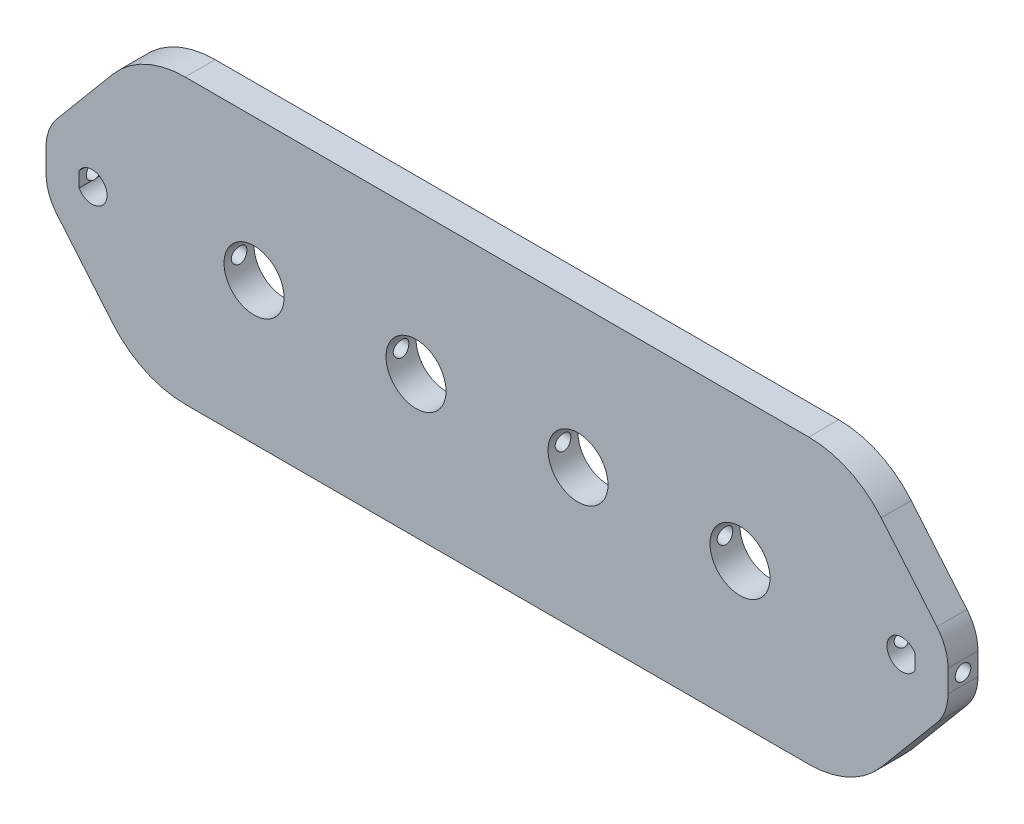
SolidWorks part; units mm, degrees
ref_plane "Front Plane" through (0, 0, 0) normal (0, 0, 1) x (1, 0, 0)
ref_plane "Top Plane" through (0, 0, 0) normal (0, 1, 0) x (1, 0, 0)
ref_plane "Right Plane" through (0, 0, 0) normal (1, 0, 0) x (0, 0, -1)
sketch "Sketch1" plane through (0, 0, 0) normal (0, 0, 1) x (1, 0, 0)
  line L0 (-85.725, 0) -> (85.725, 0) construction
  line L1 (-85.725, 30) -> (85.725, 30)
  line L2 (-85.725, -30) -> (85.725, -30)
  line L3 (0, 30) -> (0, -30) construction
  line L4 (-75.3362, 30) -> (-95.4746, 6)
  line L5 (-95.4746, 6) -> (-95.4746, -6)
  line L6 (-95.4746, -6) -> (-75.3362, -30)
  line L7 (-88.4746, -0.7777) -> (-88.4746, -1.5875) construction
  line L8 (-88.4746, -0.7777) -> (-88.4746, 0.7777) construction
  line L13 (88.4746, 1.5875) -> (88.4746, -1.5875)
  line L14 (-88.4746, 1.5875) -> (-88.4746, -1.5875)
  line L15 (95.4746, -6) -> (75.3362, -30)
  line L16 (95.4746, 6) -> (95.4746, -6)
  line L17 (75.3362, 30) -> (95.4746, 6)
  arc A0 (-85.725, 30) -> (-85.725, -30) centre (-85.725, 0) ccw
  arc A1 (85.725, -30) -> (85.725, 30) centre (85.725, 0) ccw
  arc A5 (-88.4746, -1.5875) -> (-88.4746, 1.5875) centre (-85.725, 0) ccw construction
  circle A6 centre (-88.4746, 1.5875) radius 0.25 construction
  circle A7 centre (-88.4746, -1.5875) radius 0.25 construction
  arc A13 (88.4746, 1.5875) -> (88.4746, -1.5875) centre (85.725, 0) ccw
  arc A14 (-88.4746, 1.5875) -> (-88.4746, -1.5875) centre (-85.725, 0) cw
  circle A17 centre (51.435, 0) radius 6.35
  circle A18 centre (17.145, 0) radius 6.35
  circle A19 centre (-17.145, 0) radius 6.35
  circle A20 centre (-51.435, 0) radius 6.35
  point P3 (0, 0)
  point P17 (-88.4746, 1.5619)
  point P20 (0, 0)
  point P21 (-88.4588, -1.6147)
  point P22 (-88.4746, -1.541)
  point P23 (0, 0)
  point P24 (88.4746, -1.5875)
  point P25 (88.4746, 1.5875)
  point P27 (88.4393, -1.6472)
  point P29 (-88.4746, 1.6542)
  point P37 (51.435, 0)
  point P38 (-95.4746, 0)
  point P39 (85.725, 0)
  point P40 (17.145, 0)
  point P41 (-17.145, 0)
  point P46 (-51.435, 0)
  point P53 (88.4746, 1.4927)
  point P54 (0, 0)
  point P55 (-88.4255, 1.6542)
  dimension "D2" = 0.5
  dimension "D4" = 0.5
  dimension "D9" = 12.7
  dimension "D10" = 3.175
  dimension "D1" = 171.45
  dimension "D3" = 60
  dimension "D5" = 7
  dimension "D6" = 220
  dimension "D7" = 12
  dimension "D8" = 5
extrude "Boss-Extrude1" add sketch "Sketch1" along normal mid plane 6.35
fillet "Fillet1" [suppressed] radius 2
fillet "Fillet2" radius 10 4 edges at (-95.4746, -6, 0) (-95.4746, 6, 0) (95.4746, -6, 0) (95.4746, 6, 0)
fillet "Fillet3" radius 20 4 edges at (-75.3362, 30, 0) (-75.3362, -30, 0) (75.3362, -30, 0) (75.3362, 30, 0)
hole_wizard "M4x0.7 Tapped Hole1" positions "Sketch3" profile "Sketch4" tap size "M4x0.7" standard "ANSI Metric" end condition through all
sketch "Sketch3" plane through (-95.4746, 0, 0) normal (-1, 0, 0) x (0, 0, 1)
  point P0 (0, 0)
cosmetic thread "Hole Thread1" parameters "D2"=4
sketch "Sketch4" plane through (-95.4746, 0, 0) normal (0, 1, 0) x (0, 0, 1)
  line L0 (0, 0) -> (0, 190.9493)
  line L1 (0, 190.9493) -> (1.65, 190.9493)
  line L2 (1.65, 190.9493) -> (1.65, 0)
  line L5 (1.65, 0) -> (0, 0)
  line L11 (0, -6.35) -> (0, 107.95) construction
  dimension "Thru Tap Drill Dia." = 3.3
  dimension "Thru Tap Drill Depth" = 190.9493
sketch "Sketch5" plane through (0, 0, 0) normal (0, 0, 1) x (1, 0, 0)
  line L0 (0, 30) -> (0, -30) construction
  line L1 (-66.0101, 30) -> (66.0101, 30) construction
  line L2 (-66.0101, -30) -> (66.0101, -30) construction
  line L3 (95.4746, 0) -> (-95.4746, 0) construction
  line L4 (-75.7735, 32.482) -> (-64.1475, 37.5933) construction
  line L5 (-81.331, 22.8558) -> (-93.1351, 8.7882) construction
  line L6 (-69.9605, 35.0376) -> (-67.9482, 30.4604) construction
  line L7 (-73.7612, 27.9048) -> (-62.1351, 33.0161) construction
  line L8 (-73.7612, 27.9048) -> (-62.1351, 33.0161)
  line L9 (-75.7735, 32.482) -> (-64.1475, 37.5933)
  line L10 (-43.666, 30) -> (-88.525, 14.2822)
  line L11 (69.9605, 35.0376) -> (67.9482, 30.4604) construction
  line L12 (43.666, 30) -> (88.525, 14.2822)
  line L13 (75.7735, 32.482) -> (64.1475, 37.5933)
  line L14 (73.7612, 27.9048) -> (62.1351, 33.0161)
  line L15 (95.4746, 2.3603) -> (95.4746, -2.3603) construction
  line L16 (-95.4746, 2.3603) -> (-95.4746, -2.3603) construction
  line L17 (-43.666, -30) -> (-88.525, -14.2822)
  line L18 (43.666, -30) -> (88.525, -14.2822)
  arc A0 (-43.666, 30) -> (-88.525, 14.2822) centre (-65.279, 19.8108) ccw
  arc A1 (-62.1351, 33.0161) -> (-64.1475, 37.5933) centre (-63.1413, 35.3047) ccw construction
  arc A2 (-75.7735, 32.482) -> (-73.7612, 27.9048) centre (-74.7673, 30.1934) ccw construction
  arc A3 (-75.7735, 32.482) -> (-73.7612, 27.9048) centre (-74.7673, 30.1934) ccw
  arc A4 (-62.1351, 33.0161) -> (-64.1475, 37.5933) centre (-63.1413, 35.3047) ccw
  arc A5 (62.1351, 33.0161) -> (64.1475, 37.5933) centre (63.1413, 35.3047) cw
  arc A6 (75.7735, 32.482) -> (73.7612, 27.9048) centre (74.7673, 30.1934) cw
  arc A7 (43.666, 30) -> (88.525, 14.2822) centre (65.279, 19.8108) cw
  arc A8 (-43.666, -30) -> (-88.525, -14.2822) centre (-65.279, -19.8108) cw
  arc A9 (43.666, -30) -> (88.525, -14.2822) centre (65.279, -19.8108) ccw
  point P10 (-73.1802, 42.3611)
  point P24 (-60.8527, 36.3108)
  point P32 (73.1802, 42.3611)
  dimension "D2" = 16.5
  dimension "D1" = 8
extrude "Boss-Extrude2" [suppressed] add sketch "Sketch5" along normal mid plane 6.35
fillet "Fillet4" [suppressed] radius 8
sketch "Sketch6" [suppressed] plane through (0, 0, 0) normal (0, 0, 1) x (1, 0, 0)
  line L0 (0, 30) -> (0, -30) construction
  line L1 (-39.0796, 30) -> (39.0796, 30) construction
  line L2 (-39.0796, -30) -> (39.0796, -30) construction
  line L3 (95.4746, 0) -> (-95.4746, 0) construction
  line L4 (-95.4746, 2.3603) -> (-95.4746, -2.3603) construction
  line L5 (95.4746, 2.3603) -> (95.4746, -2.3603) construction
  line L6 (-55.4603, 36.3647) -> (-82.4483, 29.1333) construction
  line L9 (-73.7612, 27.9048) -> (-62.1351, 33.0161) construction
  line L10 (-55.1316, 35.138) -> (-82.1196, 27.9066)
  line L11 (-64.1475, 37.5933) -> (-75.7735, 32.482) construction
  line L12 (-55.789, 37.5915) -> (-82.777, 30.3601)
  line L13 (-69.9605, 35.0376) -> (-67.9482, 30.4604) construction
  line L15 (-73.7612, 27.9048) -> (-62.1351, 33.0161)
  line L16 (-64.1475, 37.5933) -> (-75.7735, 32.482)
  line L17 (55.4603, 36.3647) -> (82.4483, 29.1333) construction
  line L18 (55.1316, 35.138) -> (82.1196, 27.9066)
  line L19 (55.789, 37.5915) -> (82.777, 30.3601)
  line L20 (64.1475, 37.5933) -> (75.7735, 32.482)
  line L21 (73.7612, 27.9048) -> (62.1351, 33.0161)
  line L22 (55.4603, -36.3647) -> (82.4483, -29.1333) construction
  line L23 (55.1316, -35.138) -> (82.1196, -27.9066)
  line L24 (55.789, -37.5915) -> (82.777, -30.3601)
  line L25 (-55.4603, -36.3647) -> (-82.4483, -29.1333) construction
  line L26 (-55.1316, -35.138) -> (-82.1196, -27.9066)
  line L27 (-55.789, -37.5915) -> (-82.777, -30.3601)
  arc A2 (-55.1316, 35.138) -> (-55.789, 37.5915) centre (-55.4603, 36.3647) ccw
  arc A3 (-82.777, 30.3601) -> (-82.1196, 27.9066) centre (-82.4483, 29.1333) ccw
  arc A4 (-75.7735, 32.482) -> (-73.7612, 27.9048) centre (-74.7673, 30.1934) ccw construction
  arc A5 (-62.1351, 33.0161) -> (-64.1475, 37.5933) centre (-63.1413, 35.3047) ccw construction
  arc A6 (-75.7735, 32.482) -> (-73.7612, 27.9048) centre (-74.7673, 30.1934) ccw
  arc A7 (-62.1351, 33.0161) -> (-64.1475, 37.5933) centre (-63.1413, 35.3047) ccw
  arc A8 (55.1316, 35.138) -> (55.789, 37.5915) centre (55.4603, 36.3647) cw
  arc A9 (82.777, 30.3601) -> (82.1196, 27.9066) centre (82.4483, 29.1333) cw
  arc A10 (62.1351, 33.0161) -> (64.1475, 37.5933) centre (63.1413, 35.3047) cw
  arc A11 (75.7735, 32.482) -> (73.7612, 27.9048) centre (74.7673, 30.1934) cw
  arc A12 (55.1316, -35.138) -> (55.789, -37.5915) centre (55.4603, -36.3647) ccw
  arc A13 (82.777, -30.3601) -> (82.1196, -27.9066) centre (82.4483, -29.1333) ccw
  arc A14 (-55.1316, -35.138) -> (-55.789, -37.5915) centre (-55.4603, -36.3647) cw
  arc A15 (-82.777, -30.3601) -> (-82.1196, -27.9066) centre (-82.4483, -29.1333) cw
  point P14 (-68.9543, 32.749)
  point P32 (68.9543, 32.749)
  point P45 (68.9543, -32.749)
  point P52 (-68.9543, -32.749)
  dimension "D1" = 15
  dimension "D2" = 27.94
  dimension "D3" = 2.54
extrude "Cut-Extrude1" [suppressed] cut sketch "Sketch6" against normal through all both and the other way through all contours L15 A7 L10 A6 | L19 A9 L18 A8 | L21 A10 L20 A11 | L23 A13 L24 A12 | L27 A15 L26 A14
fillet "Fillet5" [suppressed] radius 1.5
